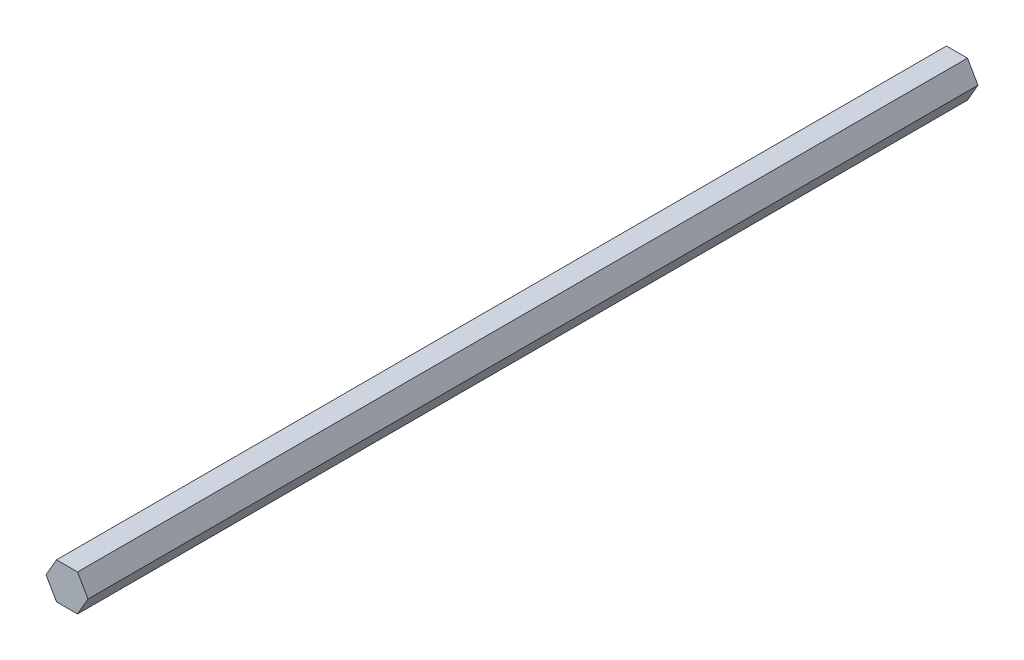
SolidWorks part; units mm, degrees
ref_plane "Front Plane" through (0, 0, 0) normal (0, 0, 1) x (1, 0, 0)
ref_plane "Top Plane" through (0, 0, 0) normal (0, 1, 0) x (1, 0, 0)
ref_plane "Right Plane" through (0, 0, 0) normal (1, 0, 0) x (0, 0, -1)
sketch "Sketch1" plane through (0, 0, 0) normal (0, 0, 1) x (1, 0, 0)
  line L1 (7.3323, 0) -> (3.6662, 6.35)
  line L2 (3.6662, 6.35) -> (-3.6662, 6.35)
  line L3 (-3.6662, 6.35) -> (-7.3323, 0)
  line L4 (-7.3323, 0) -> (-3.6662, -6.35)
  line L5 (-3.6662, -6.35) -> (3.6662, -6.35)
  line L6 (3.6662, -6.35) -> (7.3323, 0)
  circle A0 centre (0, 0) radius 6.35 construction
  dimension "D1" = 12.7
extrude "Boss-Extrude1" add sketch "Sketch1" along normal blind 310.4
